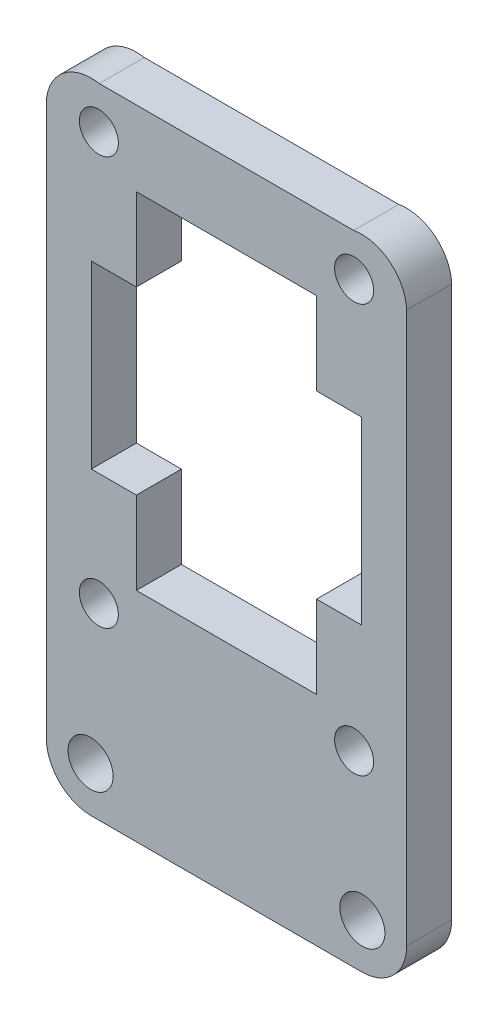
SolidWorks part; units mm, degrees
ref_plane "Front Plane" through (0, 0, 0) normal (0, 0, 1) x (1, 0, 0)
ref_plane "Top Plane" through (0, 0, 0) normal (0, 1, 0) x (1, 0, 0)
ref_plane "Right Plane" through (0, 0, 0) normal (1, 0, 0) x (0, 0, -1)
sketch "Model" plane through (0, 0, 0) normal (0, 0, 1) x (1, 0, 0)
  line L0 (69.2662, 48.75) -> (69.2662, 36.75)
  line L1 (72.2662, 46.25) -> (72.2662, 56.421)
  line L2 (48.2662, 46.25) -> (48.2662, 19.75)
  line L3 (51.2662, 16.75) -> (69.2662, 16.75)
  line L4 (51.7943, 59.25) -> (68.738, 59.25)
  line L5 (54.2662, 54.25) -> (66.2662, 54.25)
  line L6 (69.2662, 48.75) -> (66.2662, 48.75)
  line L7 (54.2662, 48.75) -> (51.2662, 48.75)
  line L8 (51.2662, 36.75) -> (54.2662, 36.75)
  line L9 (69.2662, 36.75) -> (66.2662, 36.75)
  line L10 (66.2662, 31.25) -> (54.2662, 31.25)
  line L11 (54.2662, 54.25) -> (54.2662, 48.75)
  line L12 (51.2662, 48.75) -> (51.2662, 36.75)
  line L13 (54.2662, 36.75) -> (54.2662, 31.25)
  line L14 (66.2662, 31.25) -> (66.2662, 36.75)
  line L15 (66.2662, 48.75) -> (66.2662, 54.25)
  line L17 (48.2662, 56.4071) -> (48.2662, 46.25)
  line L18 (72.2662, 46.25) -> (72.2662, 19.75)
  circle A0 centre (51.7661, 56.45) radius 1.299
  circle A1 centre (68.7662, 56.45) radius 1.299
  circle A2 centre (51.7661, 29.25) radius 1.299
  circle A3 centre (68.7661, 29.25) radius 1.299
  circle A4 centre (51.2162, 19.75) radius 1.5
  circle A5 centre (69.3162, 19.75) radius 1.5
  arc A6 (69.2662, 16.75) -> (72.2662, 19.75) centre (69.266, 19.7502) ccw
  arc A7 (48.2662, 19.75) -> (51.2662, 16.75) centre (51.2663, 19.7501) ccw
  arc A8 (51.7943, 59.25) -> (48.2662, 56.4071) centre (51.2641, 56.2973) ccw
  arc A9 (72.2662, 56.421) -> (68.738, 59.25) centre (69.2689, 56.2975) ccw
  dimension "D1" = 2.8
  dimension "D2" = 2.8
extrude "Boss-Extrude1" add sketch "Model" along normal blind 3
